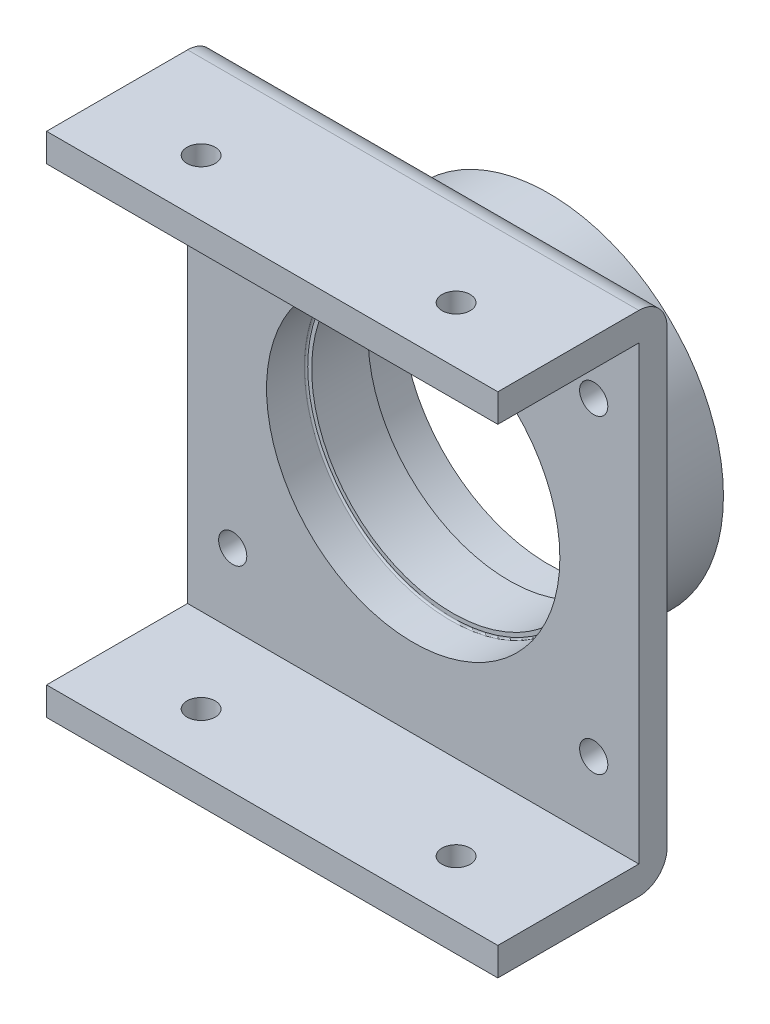
SolidWorks part; units mm, degrees
material "6061 Alloy"
ref_plane "Front Plane" through (0, 0, 0) normal (0, 0, 1) x (1, 0, 0)
ref_plane "Top Plane" through (0, 0, 0) normal (0, 1, 0) x (1, 0, 0)
ref_plane "Right Plane" through (0, 0, 0) normal (1, 0, 0) x (0, 0, -1)
sketch "Sketch1" plane through (0, 0, 0) normal (0, 0, 1) x (1, 0, 0)
  circle A0 centre (0, 0) radius 26
  circle A1 centre (0, 0) radius 31
  dimension "D1" = 52
  dimension "D2" = 5
extrude "Boss-Extrude1" add sketch "Sketch1" along normal blind 7
sketch "Sketch2" plane through (0, 0, 7) normal (0, 0, 1) x (1, 0, 0)
  circle A0 centre (0, 0) radius 31
  circle A1 centre (0, 0) radius 25
  dimension "D1" = 62
  dimension "D2" = 50
extrude "Boss-Extrude3" add sketch "Sketch2" along normal blind 10
sketch "Sketch3" plane through (0, 0, 17) normal (0, 0, 1) x (1, 0, 0)
  circle A0 centre (0, 0) radius 26
  circle A1 centre (0, 0) radius 31
  dimension "D1" = 62
  dimension "D2" = 52
extrude "Boss-Extrude4" add sketch "Sketch3" along normal blind 7
fillet "Fillet1" radius 0.3 2 edges at (26, 0, 7) (26, 0, 17)
sketch "Sketch4" plane through (0, 0, 24) normal (0, 0, 1) x (1, 0, 0)
  line L1 (-40, -40) -> (40, -40)
  line L2 (-40, -40) -> (-40, 40)
  line L3 (-40, 40) -> (40, 40)
  line L4 (40, -40) -> (40, 40)
  line L5 (-40, -40) -> (40, 40) construction
  line L6 (-40, 40) -> (40, -40) construction
  circle A0 centre (0, 0) radius 31
  dimension "D1" = 62
  dimension "D2" = 80
  dimension "D3" = 80
extrude "Boss-Extrude5" add sketch "Sketch4" against normal blind 5
fillet "Fillet2" radius 2 1 edges at (31, 0, 19)
hole_wizard "M6x1.0 Tapped Hole1" positions "Sketch5" profile "Sketch6" tap size "M6x1.0" standard "ANSI Metric" end condition through all
sketch "Sketch5" plane through (0, 0, 24) normal (0, 0, 1) x (1, 0, 0)
  line L0 (40, -40) -> (40, 40) construction
  line L2 (40, 40) -> (-40, 40) construction
  point P0 (-32, 27.5)
  point P2 (32, 27.5)
  point P4 (32, -27.5)
  point P6 (-32, -27.5)
  dimension "D1" = 64
  dimension "D2" = 8
  dimension "D3" = 55
  dimension "D4" = 12.5
sketch "Sketch6" plane through (-32, 27.5, 24) normal (1, 0, 0) x (0, -1, 0)
  line L0 (0, 0) -> (0, 24)
  line L1 (0, 24) -> (2.5, 24)
  line L2 (2.5, 24) -> (2.5, 0)
  line L5 (2.5, 0) -> (0, 0)
  line L11 (0, -6.35) -> (0, 107.95) construction
  dimension "Thread Major Dia." = 5
  dimension "Thru Tap Drill Depth" = 24
sketch "Sketch7" plane through (40, 0, 0) normal (1, 0, 0) x (0, 0, -1)
  line L0 (-24, -40) -> (-24, 40) construction
  line L1 (-19, 40) -> (-29, 40)
  line L2 (-19, 40) -> (-19, 45)
  line L3 (-19, 45) -> (-29, 45)
  line L4 (-29, 40) -> (-29, 45)
  line L6 (-19, -40) -> (-29, -40)
  line L7 (-19, -40) -> (-19, -45)
  line L8 (-19, -45) -> (-29, -45)
  line L9 (-29, -40) -> (-29, -45)
  dimension "D1" = 5
  dimension "D2" = 5
  dimension "D3" = 5
  dimension "D4" = 5
extrude "Boss-Extrude6" add sketch "Sketch7" against normal up to surface (80 mm away) up to face at (-40, 0, 21.5)
fillet "Fillet3" radius 5 2 edges at (0, -45, 19) (0, 45, 19)
sketch "Sketch8" plane through (40, 0, 0) normal (1, 0, 0) x (0, 0, -1)
  line L0 (-29, 45) -> (-49, 45)
  line L1 (-49, 45) -> (-49, 40)
  line L2 (-49, 40) -> (-29, 40)
  line L3 (-29, -40) -> (-49, -40)
  line L4 (-49, -40) -> (-49, -45)
  line L5 (-49, -45) -> (-29, -45)
  line L6 (-29, 45) -> (-29, 40)
  line L7 (-29, -40) -> (-29, -45)
  dimension "D1" = 20
  dimension "D2" = 20
extrude "Boss-Extrude7" add sketch "Sketch8" against normal up to surface (80 mm away) up to face at (-40, 0, 24.7929)
hole_wizard "M6x1.0 Tapped Hole2" positions "Sketch9" profile "Sketch10" tap size "M6x1.0" standard "ANSI Metric" end condition through all
sketch "Sketch9" plane through (0, 45, 0) normal (0, 1, 0) x (1, 0, 0)
  line L0 (-40, -49) -> (40, -49) construction
  line L1 (0, -26.95) -> (0, 26.95) construction
  point P0 (-22.6, -39)
  point P2 (22.6, -39)
  point P12 (0, 0)
  point P13 (-21.6282, -39)
  dimension "D1" = 10
  dimension "D2" = 45.2
  dimension "D3" = 22.6
sketch "Sketch10" plane through (-22.6, 45, 39) normal (1, 0, 0) x (0, 0, 1)
  line L0 (0, 0) -> (0, 90)
  line L1 (0, 90) -> (2.5, 90)
  line L2 (2.5, 90) -> (2.5, 0)
  line L5 (2.5, 0) -> (0, 0)
  line L11 (0, -6.35) -> (0, 107.95) construction
  dimension "Thru Tap Drill Dia." = 5
  dimension "Thru Tap Drill Depth" = 90
cosmetic thread "Hole Thread3" parameters "D2"=6
cosmetic thread "Hole Thread4" parameters "D2"=6
